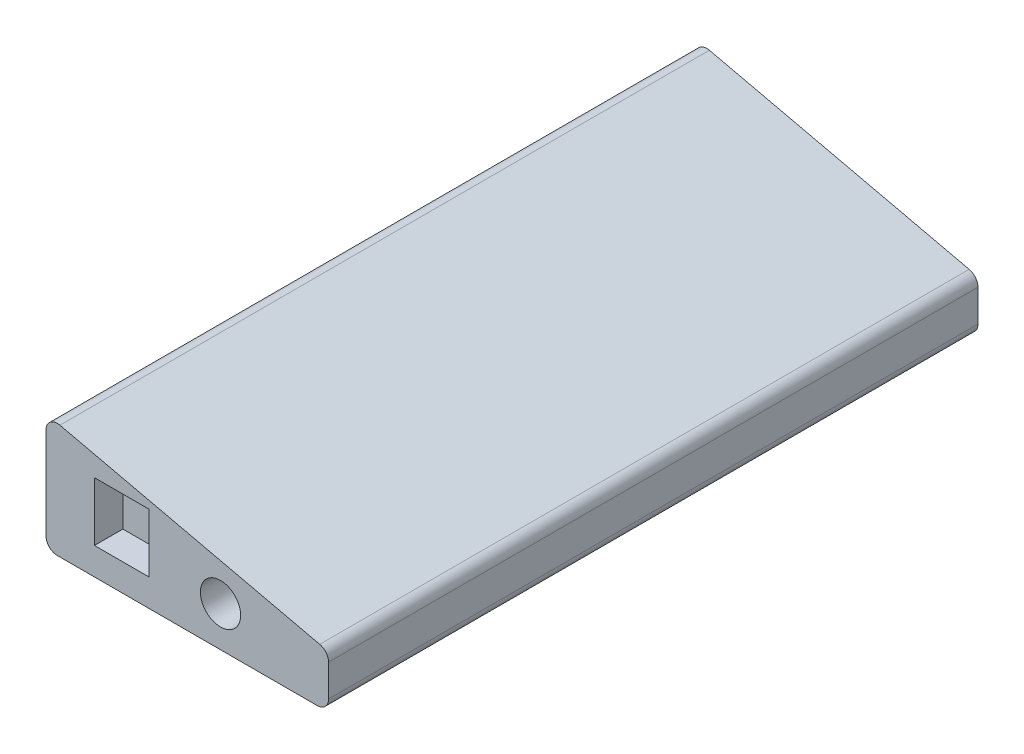
SolidWorks part; units mm, degrees
ref_plane "Front Plane" through (0, 0, 0) normal (0, 0, 1) x (1, 0, 0)
ref_plane "Top Plane" through (0, 0, 0) normal (0, 1, 0) x (1, 0, 0)
ref_plane "Right Plane" through (0, 0, 0) normal (1, 0, 0) x (0, 0, -1)
sketch "Sketch1" plane through (0, 0, 0) normal (0, 0, 1) x (1, 0, 0)
  line L0 (3.1102, 25.509) -> (61.1492, 12.1378)
  line L1 (2.54, 0) -> (60.579, 0)
  line L2 (0, 2.54) -> (0, 23.0338)
  line L4 (63.119, 2.54) -> (63.119, 9.6626)
  arc A0 (61.1492, 12.1378) -> (63.119, 9.6626) centre (60.579, 9.6626) cw
  arc A1 (60.579, 0) -> (63.119, 2.54) centre (60.579, 2.54) ccw
  arc A2 (2.54, 0) -> (0, 2.54) centre (2.54, 2.54) cw
  arc A3 (0, 23.0338) -> (3.1102, 25.509) centre (2.54, 23.0338) cw
  point P7 (63.119, 11.684)
  point P10 (63.119, 0)
  point P13 (0, 0)
  point P16 (0, 26.2255)
  dimension "D4" = 2.54
  dimension "D1" = 11.684
  dimension "D2" = 26.2255
  dimension "D3" = 63.119
extrude "Boss-Extrude1" add sketch "Sketch1" along normal blind 145.0848 contours L0 A0 L4 A1 L1 A2 L2 A3
sketch "Sketch2" plane through (0, 0, 145.0848) normal (0, 0, 1) x (1, 0, 0)
  line L1 (10.8204, 19.2151) -> (23.0124, 19.2151)
  line L2 (10.8204, 19.2151) -> (10.8204, 6.096)
  line L3 (10.8204, 6.096) -> (23.0124, 6.096)
  line L4 (23.0124, 19.2151) -> (23.0124, 6.096)
  line L5 (0, 2.54) -> (0, 23.0338) construction
  line L6 (2.54, 0) -> (60.579, 0) construction
  line L7 (63.119, 2.54) -> (63.119, 9.6626) construction
  circle A0 centre (38.989, 8.9154) radius 4.5021
  point P10 (63.119, 6.1013)
  dimension "D1" = 9.0043
  dimension "D2" = 12.192
  dimension "D3" = 13.1191
  dimension "D4" = 10.8204
  dimension "D5" = 6.096
  dimension "D6" = 24.13
  dimension "D7" = 8.9154
extrude "Cut-Extrude1" cut sketch "Sketch2" against normal blind 6.35
sketch "Sketch3" plane through (0, 0, 0) normal (-1, 0, 0) x (0, 0, 1)
  line L0 (0, 2.54) -> (0, 23.0338) construction
  line L1 (25.4, 13.1826) -> (38.5064, 13.1826)
  line L2 (25.4, 13.1826) -> (25.4, 7.1882)
  line L3 (25.4, 7.1882) -> (38.5064, 7.1882)
  line L4 (38.5064, 13.1826) -> (38.5064, 7.1882)
  line L5 (145.0848, 0) -> (0, 0) construction
  line L6 (46.482, 13.1826) -> (59.5884, 13.1826)
  line L7 (46.482, 13.1826) -> (46.482, 7.1882)
  line L8 (46.482, 7.1882) -> (59.5884, 7.1882)
  line L9 (59.5884, 13.1826) -> (59.5884, 7.1882)
  line L10 (67.564, 13.1826) -> (80.6704, 13.1826)
  line L11 (67.564, 13.1826) -> (67.564, 7.1882)
  line L12 (67.564, 7.1882) -> (80.6704, 7.1882)
  line L13 (80.6704, 13.1826) -> (80.6704, 7.1882)
  line L14 (88.646, 13.1826) -> (101.7524, 13.1826)
  line L15 (88.646, 13.1826) -> (88.646, 7.1882)
  line L16 (88.646, 7.1882) -> (101.7524, 7.1882)
  line L17 (101.7524, 13.1826) -> (101.7524, 7.1882)
  line L18 (109.728, 13.1826) -> (122.8344, 13.1826)
  line L19 (109.728, 13.1826) -> (109.728, 7.1882)
  line L20 (109.728, 7.1882) -> (122.8344, 7.1882)
  line L21 (122.8344, 13.1826) -> (122.8344, 7.1882)
  dimension "D1" = 13.1064
  dimension "D2" = 5.9944
  dimension "D3" = 25.4
  dimension "D4" = 7.1882
  dimension "D6" = 7.9756
  dimension "D5" = 5
extrude "Cut-Extrude2" cut sketch "Sketch3" against normal blind 6.35 contours L1 L4 L3 L2
sketch "Sketch4" plane through (0, 0, 0) normal (0, 0, -1) x (-1, 0, 0)
  line L0 (0, 7.1882) -> (0, 13.1826) construction
  line L1 (-7.1628, 13.1953) -> (-20.2057, 13.1953)
  line L2 (-7.1628, 13.1953) -> (-7.1628, 7.2009)
  line L3 (-7.1628, 7.2009) -> (-20.2057, 7.2009)
  line L4 (-20.2057, 13.1953) -> (-20.2057, 7.2009)
  line L5 (-2.54, 0) -> (-60.579, 0) construction
  line L6 (0, 2.54) -> (0, 23.0338) construction
  line L7 (-28.4988, 13.1953) -> (-41.5417, 13.1953)
  line L8 (-28.4988, 13.1953) -> (-28.4988, 7.2009)
  line L9 (-28.4988, 7.2009) -> (-41.5417, 7.2009)
  line L10 (-41.5417, 13.1953) -> (-41.5417, 7.2009)
  dimension "D1" = 13.0429
  dimension "D2" = 7.2009
  dimension "D3" = 7.1628
  dimension "D5" = 8.2931
  dimension "D4" = 2
extrude "Cut-Extrude3" cut sketch "Sketch4" against normal blind 6.35
